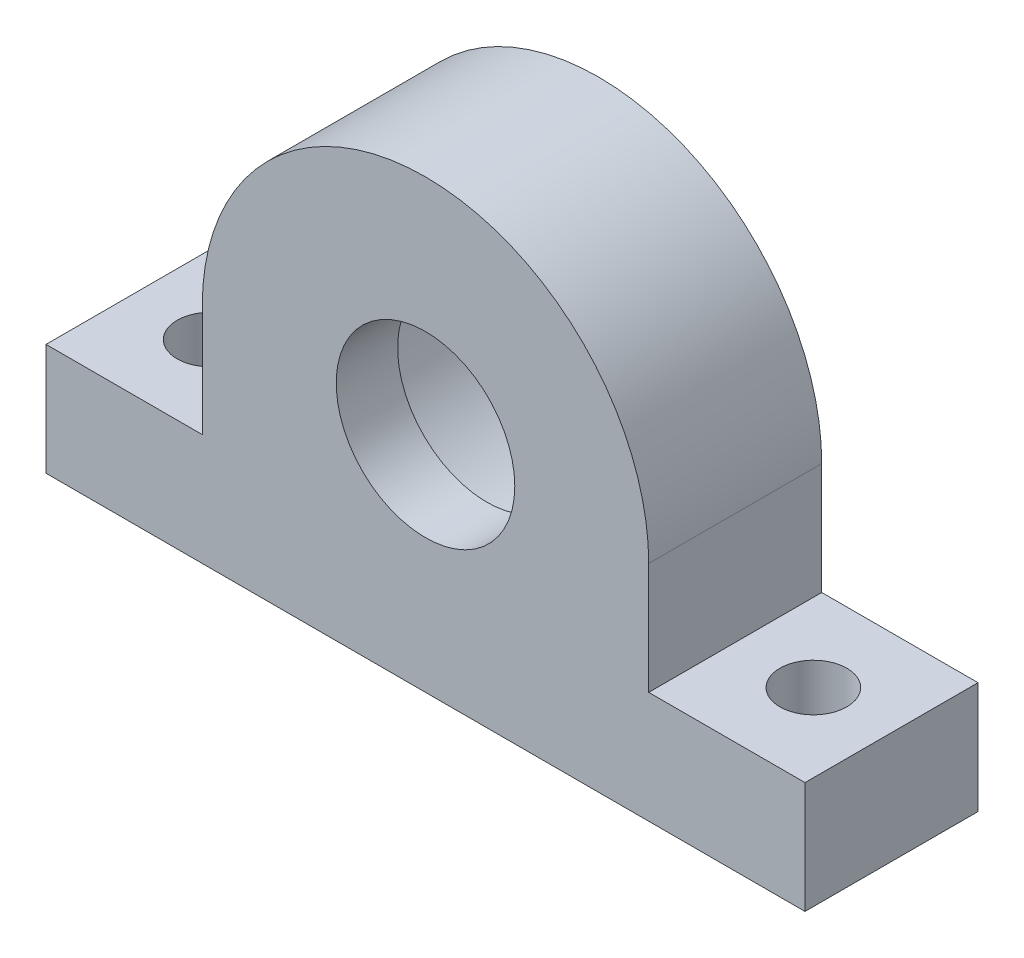
SolidWorks part; units mm, degrees
ref_plane "Front Plane" through (0, 0, 0) normal (0, 0, 1) x (1, 0, 0)
ref_plane "Top Plane" through (0, 0, 0) normal (0, 1, 0) x (1, 0, 0)
ref_plane "Right Plane" through (0, 0, 0) normal (1, 0, 0) x (0, 0, -1)
sketch "Sketch1" plane through (0, 0, 0) normal (0, 0, 1) x (1, 0, 0)
  line L0 (-34, 0) -> (34, 0)
  line L1 (34, 0) -> (34, 10)
  line L2 (34, 10) -> (20, 10)
  line L3 (20, 10) -> (20, 20)
  line L4 (0, -55) -> (0, 55) construction
  line L5 (-20, 10) -> (-20, 20)
  line L6 (-34, 10) -> (-20, 10)
  line L7 (-34, 0) -> (-34, 10)
  arc A0 (20, 20) -> (-20, 20) centre (0, 20) ccw
  circle A1 centre (0, 20) radius 13.05
  point P16 (0, 0)
  dimension "D2" = 20
  dimension "D1" = 26.1
  dimension "10" = 10
  dimension "D3" = 34
  dimension "D4" = 20
extrude "Boss-Extrude1" add sketch "Sketch1" along normal blind 10
sketch "Sketch2" plane through (0, 0, 10) normal (0, 0, 1) x (1, 0, 0)
  line L7 (34, 0) -> (34, 10)
  line L8 (34, 10) -> (20, 10)
  line L9 (20, 10) -> (20, 20)
  line L10 (-20, 20) -> (-20, 10)
  line L11 (-20, 10) -> (-34, 10)
  line L12 (-34, 10) -> (-34, 0)
  line L13 (-34, 0) -> (34, 0)
  line L14 (34, 0) -> (34, 10)
  line L15 (34, 10) -> (20, 10)
  line L16 (20, 10) -> (20, 20)
  line L17 (-20, 20) -> (-20, 10)
  line L18 (-20, 10) -> (-34, 10)
  line L19 (-34, 10) -> (-34, 0)
  line L20 (-34, 0) -> (34, 0)
  circle A0 centre (0, 20) radius 8
  arc A1 (20, 20) -> (-20, 20) centre (0, 20) ccw
  arc A2 (20, 20) -> (-20, 20) centre (0, 20) ccw
  dimension "D2" = 16
  dimension "D1" = 0
extrude "Boss-Extrude2" add sketch "Sketch2" along normal blind 5.5
sketch "Sketch3" plane through (0, 10, 0) normal (0, 1, 0) x (1, 0, 0)
  line L0 (-20, -15.5) -> (-34, 0) construction
  line L1 (20, -15.5) -> (34, 0) construction
  circle A0 centre (27, -7.75) radius 3
  circle A1 centre (-27, -7.75) radius 3
  point P13 (-27, -7.75)
  point P15 (27, -7.75)
  dimension "D1" = 6
  dimension "D2" = 6
extrude "Cut-Extrude1" cut sketch "Sketch3" against normal through all
